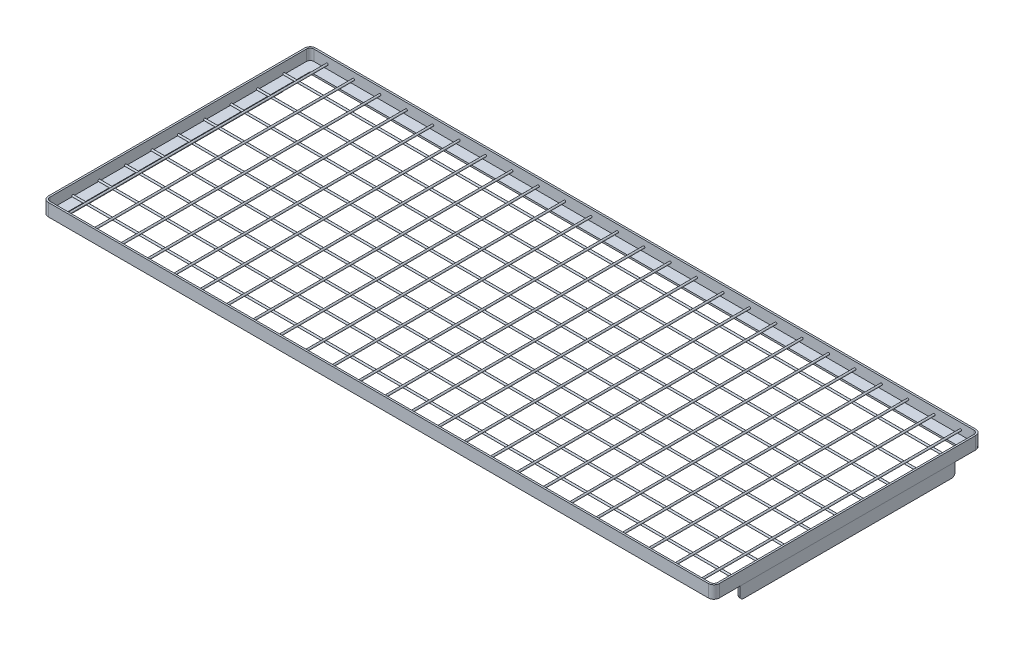
SolidWorks part; units mm, degrees
ref_plane "Front Plane" through (0, 0, 0) normal (0, 0, 1) x (1, 0, 0)
ref_plane "Top Plane" through (0, 0, 0) normal (0, 1, 0) x (1, 0, 0)
ref_plane "Right Plane" through (0, 0, 0) normal (1, 0, 0) x (0, 0, -1)
sketch "Sketch1" plane through (0, 0, 0) normal (0, 1, 0) x (1, 0, 0)
  line L0 (-667.0675, -270.256) -> (667.0675, -270.256)
  line L1 (-667.0675, -266.7) -> (667.0675, -266.7)
  line L2 (-674.6875, -259.08) -> (-674.6875, 259.08)
  line L3 (-667.0675, 266.7) -> (667.0675, 266.7)
  line L4 (674.6875, -259.08) -> (674.6875, 259.08)
  line L5 (678.2435, -259.08) -> (678.2435, 259.08)
  line L6 (-667.0675, 270.256) -> (667.0675, 270.256)
  line L7 (-678.2435, -259.08) -> (-678.2435, 259.08)
  arc A0 (-667.0675, 266.7) -> (-674.6875, 259.08) centre (-667.0675, 259.08) ccw
  arc A1 (-674.6875, -259.08) -> (-667.0675, -266.7) centre (-667.0675, -259.08) ccw
  arc A2 (667.0675, -266.7) -> (674.6875, -259.08) centre (667.0675, -259.08) ccw
  arc A3 (674.6875, 259.08) -> (667.0675, 266.7) centre (667.0675, 259.08) ccw
  arc A4 (667.0675, -270.256) -> (678.2435, -259.08) centre (667.0675, -259.08) ccw
  arc A5 (678.2435, 259.08) -> (667.0675, 270.256) centre (667.0675, 259.08) ccw
  arc A6 (-667.0675, 270.256) -> (-678.2435, 259.08) centre (-667.0675, 259.08) ccw
  arc A7 (-678.2435, -259.08) -> (-667.0675, -270.256) centre (-667.0675, -259.08) ccw
  point P0 (0, 0)
  dimension "D1" = 1349.375
  dimension "D2" = 533.4
  dimension "D3" = 3.556
extrude "Boss-Extrude1" add sketch "Sketch1" along normal blind 21.844
sketch "Sketch3" plane through (0, 0, 0) normal (0, -1, 0) x (1, 0, 0)
  line L0 (652.8435, 244.856) -> (652.8435, -244.856)
  line L1 (-667.0675, 270.256) -> (667.0675, 270.256)
  line L2 (-678.2435, 259.08) -> (-678.2435, -259.08)
  line L3 (-667.0675, -270.256) -> (667.0675, -270.256)
  line L4 (678.2435, 259.08) -> (678.2435, -259.08)
  line L5 (-678.2435, 270.256) -> (678.2435, -270.256) construction
  line L6 (-678.2435, -270.256) -> (673.3657, 268.3123) construction
  line L7 (-652.8435, -244.856) -> (652.8435, -244.856)
  line L8 (-652.8435, 244.856) -> (-652.8435, -244.856)
  line L9 (-652.8435, 244.856) -> (652.8435, 244.856)
  line L10 (-678.2435, 270.256) -> (678.2435, 270.256) construction
  line L11 (678.2435, 270.256) -> (678.2435, -270.256) construction
  line L12 (-678.2435, -270.256) -> (678.2435, -270.256) construction
  line L13 (-678.2435, 270.256) -> (-678.2435, -270.256) construction
  arc A0 (678.2435, 259.08) -> (667.0675, 270.256) centre (667.0675, 259.08) ccw
  arc A1 (667.0675, -270.256) -> (678.2435, -259.08) centre (667.0675, -259.08) ccw
  arc A2 (-678.2435, -259.08) -> (-667.0675, -270.256) centre (-667.0675, -259.08) ccw
  arc A3 (-667.0675, 270.256) -> (-678.2435, 259.08) centre (-667.0675, 259.08) ccw
  point P0 (0, 0)
  dimension "D1" = 25.4
extrude "Boss-Extrude2" add sketch "Sketch3" along normal blind 3.556
sketch "Sketch10" plane through (-674.6875, 0, 0) normal (1, 0, 0) x (0, 0, -1)
  line L1 (-259.08, -3.556) -> (259.08, -3.556) construction
  circle A0 centre (0, 1.524) radius 1.905
  dimension "D1" = 3.81
  dimension "D2" = 5.08
  dimension "D3" = 259.08
extrude "Boss-Extrude13" add sketch "Sketch10" along normal up to next (1349.375 mm away)
pattern_linear "LPattern1" count 5 spacing 53.34 along (0, 0, 1) count 5 spacing 53.34 along (0, 0, -1) of "Boss-Extrude13"
sketch "Sketch8" plane through (-678.2435, 0, 0) normal (-1, 0, 0) x (0, 0, 1)
  line L0 (-259.08, 21.844) -> (259.08, -3.556) construction
  line L1 (259.08, -3.556) -> (-259.08, -3.556) construction
  line L2 (0, 9.144) -> (0, -113.0774) construction
  line L4 (-217.4875, -28.956) -> (217.4875, -28.956)
  line L5 (-217.4875, -28.956) -> (-217.4875, -3.556)
  line L6 (-217.4875, -3.556) -> (217.4875, -3.556)
  line L7 (217.4875, -28.956) -> (217.4875, -3.556)
  line L8 (-217.4875, -28.956) -> (217.4875, -3.556) construction
  line L9 (-217.4875, -3.556) -> (217.4875, -28.956) construction
  point P8 (0, -16.256)
  dimension "D1" = 434.975
  dimension "D2" = 25.4
extrude "Boss-Extrude11" add sketch "Sketch8" against normal blind 3.556 separate body
sketch "Sketch11" plane through (0, 0, 266.7) normal (0, 0, -1) x (-1, 0, 0)
  line L0 (667.0675, 0) -> (-667.0675, 0) construction
  circle A0 centre (0, 8.89) radius 1.905
  dimension "D1" = 3.81
  dimension "D2" = 8.89
extrude "Boss-Extrude14" add sketch "Sketch11" along normal up to next (533.4 mm away)
pattern_linear "LPattern2" count 13 spacing 53.34 along (-1, 0, 0) count 13 spacing 53.34 along (1, 0, 0) of "Boss-Extrude14"
sketch "Sketch9" plane through (678.2435, 0, 0) normal (1, 0, 0) x (0, 0, -1)
  line L0 (0, -3.556) -> (0, -163.5002) construction
  line L1 (-217.4875, -3.556) -> (217.4875, -3.556) construction
  line L2 (259.08, -3.556) -> (-259.08, -3.556) construction
  line L3 (-217.4875, -28.956) -> (217.4875, -28.956)
  line L4 (-217.4875, -28.956) -> (-217.4875, -3.556)
  line L5 (-217.4875, -3.556) -> (217.4875, -3.556)
  line L6 (217.4875, -28.956) -> (217.4875, -3.556)
  line L7 (-217.4875, -28.956) -> (217.4875, -3.556) construction
  line L8 (-217.4875, -3.556) -> (217.4875, -28.956) construction
  point P5 (0, -16.256)
  dimension "D1" = 25.4
  dimension "D2" = 434.975
extrude "Boss-Extrude12" add sketch "Sketch9" against normal blind 3.556 separate body
fillet "Fillet1" radius 7.62 2 edges at (-676.4655, -28.956, 217.4875) (-676.4655, -28.956, -217.4875)
fillet "Fillet2" radius 7.62 2 edges at (676.4655, -28.956, -217.4875) (676.4655, -28.956, 217.4875)
